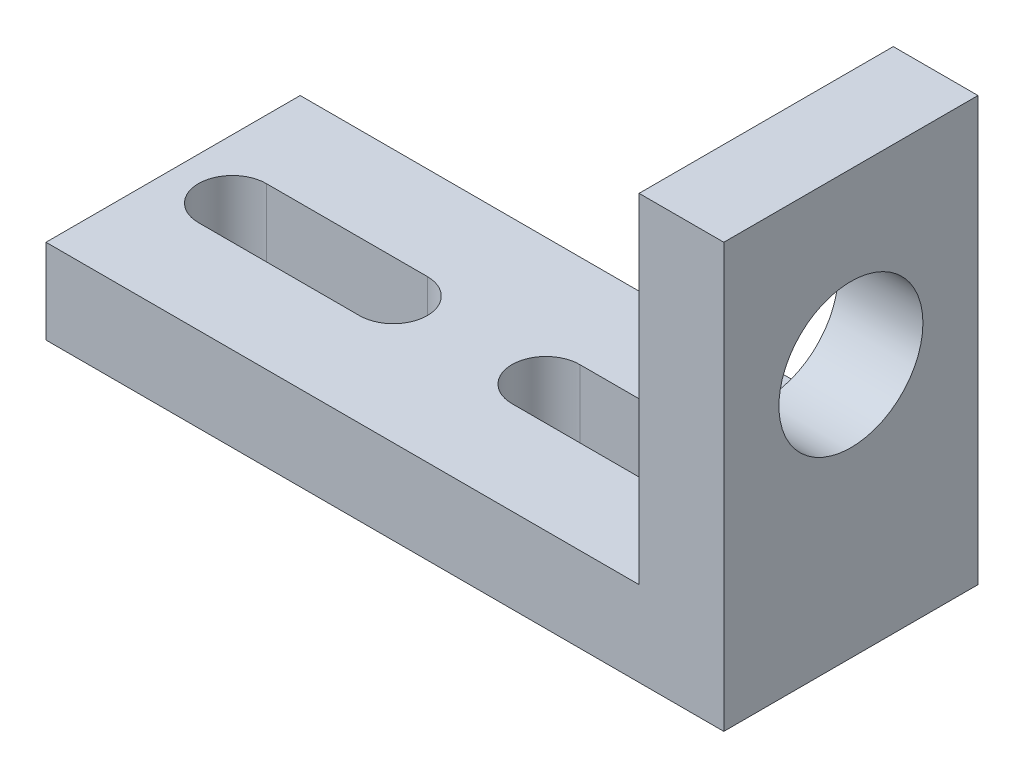
SolidWorks part; units mm, degrees
ref_plane "Front Plane" through (0, 0, 0) normal (0, 0, 1) x (1, 0, 0)
ref_plane "Top Plane" through (0, 0, 0) normal (0, 1, 0) x (1, 0, 0)
ref_plane "Right Plane" through (0, 0, 0) normal (1, 0, 0) x (0, 0, -1)
sketch "Croquis1" plane through (0, 0, 0) normal (0, 1, 0) x (1, 0, 0)
  line L0 (-20, -7.5) -> (20, -7.5)
  line L1 (-20, -7.5) -> (-20, 7.5)
  line L2 (20, -7.5) -> (20, 7.5)
  line L3 (-20, 7.5) -> (20, 7.5)
  line L4 (-20, -7.5) -> (20, 7.5) construction
  line L5 (20, -7.5) -> (-20, 7.5) construction
  point P1 (0, 0)
  dimension "D1" = 40
  dimension "D2" = 15
extrude "Saliente-Extruir1" add sketch "Croquis1" along normal blind 5
sketch "Croquis2" plane through (0, 5, 0) normal (0, 1, 0) x (1, 0, 0)
  line L0 (20, -7.5) -> (15, -7.5)
  line L1 (-20, -7.5) -> (20, -7.5) construction
  line L2 (15, -7.5) -> (15, 7.5)
  line L3 (20, 7.5) -> (-20, 7.5) construction
  line L4 (15, 7.5) -> (20, 7.5)
  line L5 (20, 7.5) -> (20, -7.5)
  dimension "D1" = 5
extrude "Saliente-Extruir2" add sketch "Croquis2" along normal blind 20
sketch "Croquis3" plane through (20, 0, 0) normal (1, 0, 0) x (0, 0, -1)
  line L0 (-7.5, 25) -> (-7.5, 5) construction
  line L1 (-7.5, 25) -> (-7.5, 0) construction
  circle A0 centre (0, 15) radius 4.25
  point P4 (-7.5, 15)
  dimension "D1" = 8.5
  dimension "D2" = 7.5
extrude "Cortar-Extruir1" cut sketch "Croquis3" against normal blind 20
sketch "Croquis4" plane through (0, 5, 0) normal (0, 1, 0) x (1, 0, 0)
  line L5 (-20, -7.5) -> (15, -7.5) construction
  line L7 (-20, 7.5) -> (-20, -7.5) construction
  line L8 (-16.5, 2) -> (-7, 2)
  line L9 (-16.5, -2) -> (-7, -2)
  line L10 (-20, 7.5) -> (15, 7.5) construction
  line L11 (-2.5, 7.5) -> (-2.5, -2.9879) construction
  line L12 (11.5, -2) -> (2, -2)
  line L13 (11.5, 2) -> (2, 2)
  arc A4 (-16.5, 2) -> (-16.5, -2) centre (-16.5, 0) ccw
  arc A5 (-7, -2) -> (-7, 2) centre (-7, 0) ccw
  arc A6 (11.5, 2) -> (11.5, -2) centre (11.5, 0) cw
  arc A7 (2, -2) -> (2, 2) centre (2, 0) cw
  dimension "D1" = 4
  dimension "D2" = 7.5
  dimension "D6" = 4
  dimension "D3" = 7.5
  dimension "D4" = 7
  dimension "D5" = 3.5
  dimension "D7" = 9.5
extrude "Cortar-Extruir2" cut sketch "Croquis4" against normal blind 20
